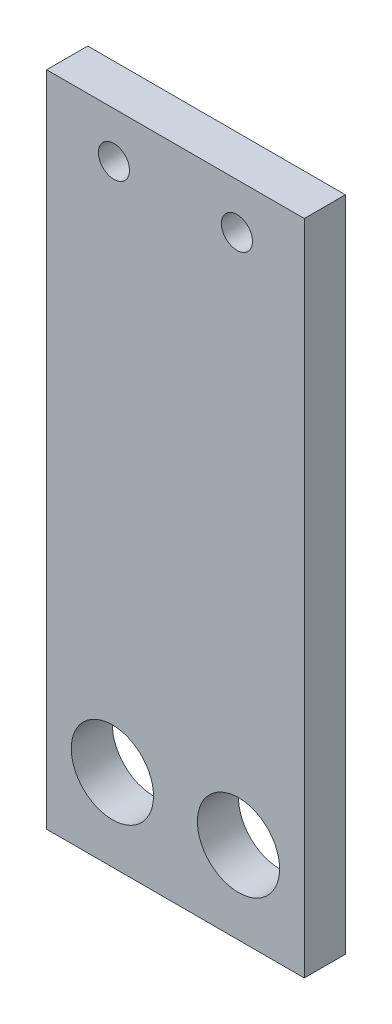
SolidWorks part; units mm, degrees
ref_plane "Front Plane" through (0, 0, 0) normal (0, 0, 1) x (1, 0, 0)
ref_plane "Top Plane" through (0, 0, 0) normal (0, 1, 0) x (1, 0, 0)
ref_plane "Right Plane" through (0, 0, 0) normal (1, 0, 0) x (0, 0, -1)
sketch "Sketch1" plane through (0, 0, 0) normal (0, 0, 1) x (1, 0, 0)
  line L1 (-9.046, 15.7038) -> (10.854, 15.7038)
  line L2 (-9.046, 15.7038) -> (-9.046, -35.0962)
  line L3 (-9.046, -35.0962) -> (10.854, -35.0962)
  line L4 (10.854, 15.7038) -> (10.854, -35.0962)
  circle A0 centre (-3.846, 12.1721) radius 1.2
  circle A1 centre (5.654, 12.1721) radius 1.2
  circle A2 centre (-3.966, -28.7462) radius 3.175
  circle A3 centre (5.774, -28.7462) radius 3.175
  point P12 (0, 0)
  dimension "D3" = 2.4
  dimension "D4" = 2.4
  dimension "D6" = 5.2
  dimension "D7" = 6.35
  dimension "D8" = 6.35
  dimension "D1" = 19.9
  dimension "D2" = 50.8
  dimension "D5" = 9.5
  dimension "D9" = 5.08
  dimension "D10" = 5.08
  dimension "D11" = 6.35
  dimension "D12" = 6.35
extrude "Boss-Extrude1" add sketch "Sketch1" along normal blind 3.175
